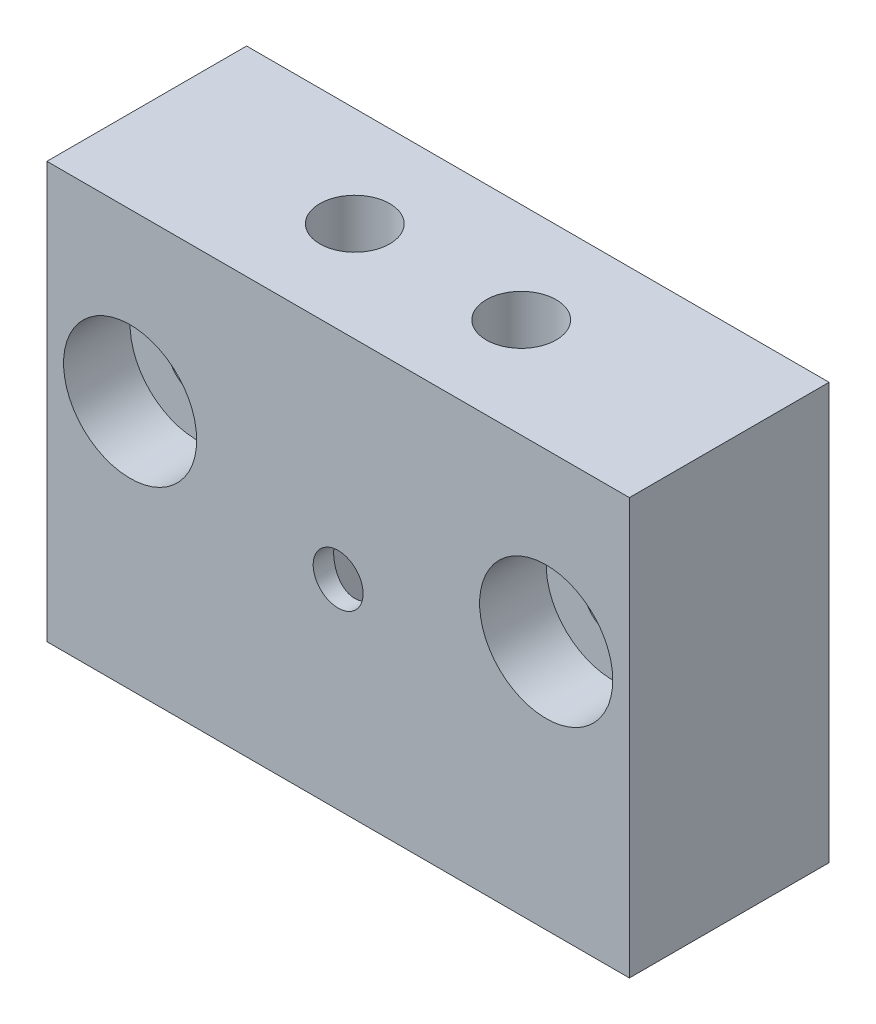
SolidWorks part; units mm, degrees
ref_plane "Front Plane" through (0, 0, 0) normal (0, 0, 1) x (1, 0, 0)
ref_plane "Top Plane" through (0, 0, 0) normal (0, 1, 0) x (1, 0, 0)
ref_plane "Right Plane" through (0, 0, 0) normal (1, 0, 0) x (0, 0, -1)
sketch "Sketch1" plane through (0, 0, 0) normal (0, 1, 0) x (1, 0, 0)
  line L0 (-17.5, 6) -> (17.5, -6) construction
  line L1 (-17.5, 6) -> (17.5, 6)
  line L2 (-17.5, 6) -> (-17.5, -6)
  line L3 (-17.5, -6) -> (17.5, -6)
  line L4 (17.5, 6) -> (17.5, -6)
  dimension "D1" = 35
  dimension "D2" = 12
extrude "Boss-Extrude1" add sketch "Sketch1" along normal blind 25
sketch "Sketch2" plane through (0, 0, 0) normal (0, -1, 0) x (1, 0, 0)
  circle A0 centre (0, 0) radius 5
  dimension "D1" = 10
extrude "Cut-Extrude1" cut sketch "Sketch2" against normal blind 18
sketch "Sketch3" plane through (0, 25, 0) normal (0, 1, 0) x (1, 0, 0)
  line L0 (-5, 0) -> (5, 0) construction
  circle A0 centre (-5, 0) radius 2.1
  circle A1 centre (5, 0) radius 2.1
  dimension "D1" = 4.2
  dimension "D2" = 10
extrude "Cut-Extrude2" cut sketch "Sketch3" against normal blind 15
sketch "Sketch4" plane through (0, 0, 6) normal (0, 0, 1) x (1, 0, 0)
  line L0 (0, 12) -> (0, 0) construction
  circle A0 centre (0, 12) radius 1.5
  dimension "D1" = 3
  dimension "D2" = 12
extrude "Cut-Extrude3" cut sketch "Sketch4" against normal blind 7
sketch "Sketch5" plane through (0, 0, 6) normal (0, 0, 1) x (1, 0, 0)
  line L0 (-12.5, 15) -> (12.5, 15) construction
  line L1 (0, 15) -> (0, 0) construction
  circle A0 centre (-12.5, 15) radius 1.75
  circle A1 centre (12.5, 15) radius 1.75
  dimension "D2" = 3.5
  dimension "D1" = 25
  dimension "D3" = 15
extrude "Cut-Extrude4" cut sketch "Sketch5" against normal through all
sketch "Sketch6" plane through (0, 0, 6) normal (0, 0, 1) x (1, 0, 0)
  circle A0 centre (-12.5, 15) radius 4
  circle A1 centre (12.5, 15) radius 4
  dimension "D1" = 8
extrude "Cut-Extrude5" cut sketch "Sketch6" against normal blind 4
